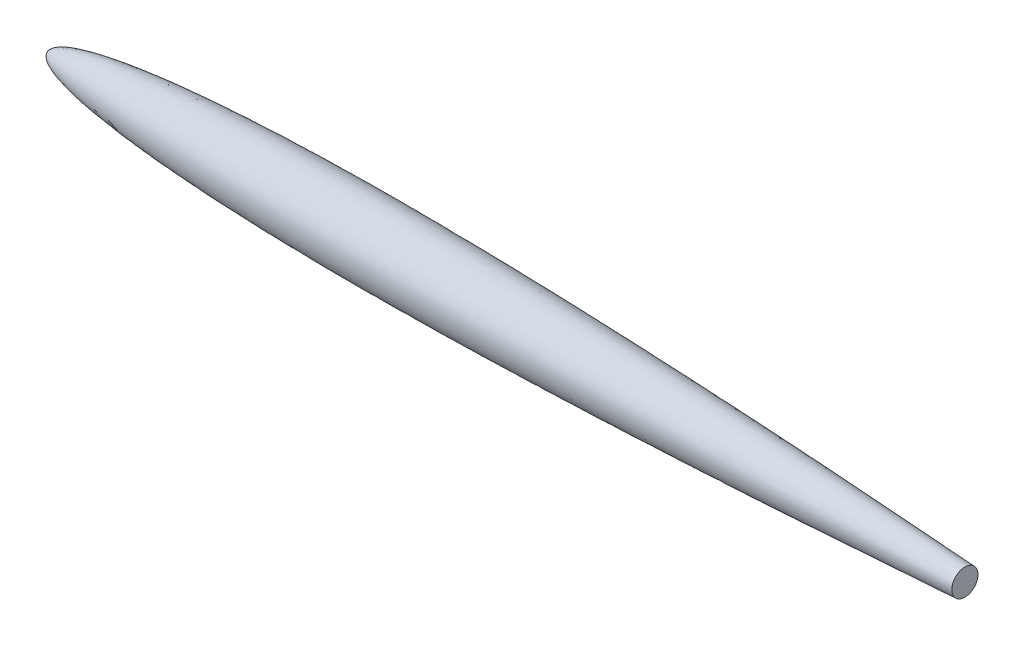
SolidWorks part; units mm, degrees
ref_plane "Front Plane" through (0, 0, 0) normal (0, 0, 1) x (1, 0, 0)
ref_plane "Top Plane" through (0, 0, 0) normal (0, 1, 0) x (1, 0, 0)
ref_plane "Right Plane" through (0, 0, 0) normal (1, 0, 0) x (0, 0, -1)
sketch "rootSketch" plane through (0, 0, 0) normal (0, 1, 0) x (1, 0, 0)
  line L0 (0, 0) -> (12000, 0) construction
  line L1 (2750, -330) -> (2750, 330) construction
  line L2 (0, 0) -> (11000, 0)
  spline S0 degree 4 poles (0, 0) (0.0002, 1.4166) (0.1225, 4.2408) (0.6739, 8.4547) (2.1097, 13.9385) (4.13, 19.1147) (6.6109, 23.9643) (9.9914, 29.3681) (13.8074, 34.3715) (18.0051, 39.0824) (24.0066, 45.0125) (32.3839, 52.2354) (43.384, 60.1944) (57.0761, 68.6181) (73.983, 77.7243) (92.7893, 86.6435) (113.9578, 95.5167) (137.4556, 104.3111) (166.2995, 114.136) (201.291, 124.8338) (243.0702, 136.2047) (291.673, 147.964) (341.2433, 158.778) (390.608, 168.603) (439.7192, 177.609) (500.6517, 187.9807) (573.4692, 199.2826) (658.6122, 211.1866) (758.0842, 223.6079) (859.6848, 234.9957) (963.387, 245.4645) (1069.1706, 255.1028) (1175.0326, 263.8354) (1280.9578, 271.7615) (1386.9346, 278.9616) (1492.954, 285.5022) (1625.577, 292.9263) (1784.8272, 300.7239) (1970.7211, 308.3762) (2183.2661, 315.3874) (2395.8558, 320.8604) (2608.4762, 324.9557) (2821.1167, 327.8069) (3033.7692, 329.5269) (3299.5919, 330.3841) (3618.5808, 329.5138) (3990.7204, 326.0523) (4415.9852, 319.2091) (4841.2016, 309.8574) (5266.3634, 298.3074) (5691.4677, 284.8151) (6116.5132, 269.5907) (6541.4998, 252.8057) (6966.4276, 234.5973) (7391.2968, 215.0715) (7816.1072, 194.3061) (8187.764, 175.0965) (8506.2884, 157.9049) (8771.6988, 143.0951) (8984.0106, 130.9561) (9196.3055, 118.5234) (9382.048, 107.3844) (9541.2445, 97.6474) (9673.9002, 89.4049) (9780.02, 82.7331) (9912.6633, 74.2947) (10032.035, 66.5803) (10138.1364, 59.6277) (10230.971, 53.4713) (10284.0168, 49.9324) (10337.0641, 46.3721) (10390.1043, 42.7909) (10443.153, 39.1874) (10496.1834, 35.5635) (10549.2402, 31.9155) (10602.2495, 28.2488) (10655.3329, 24.5543) (10708.2897, 20.8463) (10761.4536, 17.1004) (10814.2582, 13.3575) (10861.0394, 10.0201) (10900.2084, 7.2123) (10934.3368, 4.7545) (10958.871, 2.9835) (10991.7181, 0.6028) (11015.0262, -1.0918) (11049.9588, -3.6388) (11071.8096, -5.2409) (11099.5819, -7.2784) (11124.1625, -9.0892) (11155.0411, -11.3693) (11188.9639, -13.8862) (11223.5859, -16.4645) (11266.4367, -19.6696) (11318.0968, -23.5545) (11369.6077, -27.4555) (11421.2086, -31.3904) (11472.7604, -35.3439) (11524.3346, -39.3212) (11584.4862, -43.9929) (11670.4236, -50.7243) (11756.3495, -57.532) (11842.2728, -64.4184) (11928.1873, -71.3847) (11996.9163, -77.0066) (12048.459, -81.2601) (12082.8201, -84.1126) (12100, -85.543) knots 0 0 0 0 0 0.000464 0.000929 0.001393 0.001858 0.002287 0.002716 0.003486 0.003922 0.004359 0.005488 0.007118 0.008378 0.009638 0.011797 0.013955 0.015919 0.017882 0.02181 0.025978 0.030146 0.034314 0.038482 0.042518 0.046554 0.054626 0.062698 0.07077 0.079497 0.088224 0.096952 0.105679 0.114406 0.123133 0.13186 0.140587 0.158059 0.17553 0.193002 0.210474 0.227946 0.245418 0.26289 0.280362 0.315306 0.35025 0.385194 0.420137 0.455081 0.490025 0.524969 0.559913 0.594857 0.6298 0.664744 0.699688 0.71716 0.734632 0.752104 0.769576 0.787048 0.795784 0.80452 0.813256 0.821992 0.839464 0.843832 0.8482 0.852567 0.856935 0.861303 0.865671 0.870039 0.874407 0.878775 0.883143 0.887511 0.891879 0.896247 0.900615 0.902799 0.904983 0.907167 0.909351 0.912184 0.915017 0.916433 0.91785 0.920682 0.923515 0.926348 0.929181 0.932013 0.937679 0.943345 0.946177 0.94901 0.954676 0.960341 0.966007 0.977338 0.983003 0.988669 0.994334 1 1 1 1 1 construction
  spline S1 degree 4 poles (0, 0) (0.0002, 1.4166) (0.1225, 4.2408) (0.6739, 8.4547) (2.1097, 13.9385) (4.13, 19.1147) (6.6109, 23.9643) (9.9914, 29.3681) (13.8074, 34.3715) (18.0051, 39.0824) (24.0066, 45.0125) (32.3839, 52.2354) (43.384, 60.1944) (57.0761, 68.6181) (73.983, 77.7243) (92.7893, 86.6435) (113.9578, 95.5167) (137.4556, 104.3111) (166.2995, 114.136) (201.291, 124.8338) (243.0702, 136.2047) (291.673, 147.964) (341.2433, 158.778) (390.608, 168.603) (439.7192, 177.609) (500.6517, 187.9807) (573.4692, 199.2826) (658.6122, 211.1866) (758.0842, 223.6079) (859.6848, 234.9957) (963.387, 245.4645) (1069.1706, 255.1028) (1175.0326, 263.8354) (1280.9578, 271.7615) (1386.9346, 278.9616) (1492.954, 285.5022) (1625.577, 292.9263) (1784.8272, 300.7239) (1970.7211, 308.3762) (2183.2661, 315.3874) (2395.8558, 320.8604) (2608.4762, 324.9557) (2821.1167, 327.8069) (3033.7692, 329.5269) (3299.5919, 330.3841) (3618.5808, 329.5138) (3990.7204, 326.0523) (4415.9852, 319.2091) (4841.2016, 309.8574) (5266.3634, 298.3074) (5691.4677, 284.8151) (6116.5132, 269.5907) (6541.4998, 252.8057) (6966.4276, 234.5973) (7391.2968, 215.0715) (7816.1072, 194.3061) (8187.764, 175.0965) (8506.2884, 157.9049) (8771.6988, 143.0951) (8984.0106, 130.9561) (9196.3055, 118.5234) (9382.048, 107.3844) (9541.2445, 97.6474) (9673.9002, 89.4049) (9780.02, 82.7331) (9912.6633, 74.2947) (10032.035, 66.5803) (10138.1364, 59.6277) (10230.971, 53.4713) (10284.0168, 49.9324) (10337.0641, 46.3721) (10390.1043, 42.7909) (10443.153, 39.1874) (10496.1834, 35.5635) (10549.2402, 31.9155) (10602.2495, 28.2488) (10655.3329, 24.5543) (10708.2897, 20.8463) (10761.4536, 17.1004) (10814.2582, 13.3575) (10861.0394, 10.0201) (10900.2084, 7.2123) (10934.3368, 4.7545) (10958.871, 2.9835) (10981.8033, 1.3214) (10993.9727, 0.438) (11000, 0) knots 0 0 0 0 0 0.000464 0.000929 0.001393 0.001858 0.002287 0.002716 0.003486 0.003922 0.004359 0.005488 0.007118 0.008378 0.009638 0.011797 0.013955 0.015919 0.017882 0.02181 0.025978 0.030146 0.034314 0.038482 0.042518 0.046554 0.054626 0.062698 0.07077 0.079497 0.088224 0.096952 0.105679 0.114406 0.123133 0.13186 0.140587 0.158059 0.17553 0.193002 0.210474 0.227946 0.245418 0.26289 0.280362 0.315306 0.35025 0.385194 0.420137 0.455081 0.490025 0.524969 0.559913 0.594857 0.6298 0.664744 0.699688 0.71716 0.734632 0.752104 0.769576 0.787048 0.795784 0.80452 0.813256 0.821992 0.839464 0.843832 0.8482 0.852567 0.856935 0.861303 0.865671 0.870039 0.874407 0.878775 0.883143 0.887511 0.891879 0.896247 0.900615 0.902799 0.904983 0.907167 0.909351 0.909351 0.909351 0.909351 0.909351
  point P5 (2750, 0)
  dimension "rootQuarterChord" = 2750
  dimension "rootMaxThickness" = 660
revolve "Revolve1" add sketch "rootSketch" angle 360 about L0
ref_plane "Plane1" through (9020, 0, 0) normal (1, 0, 0) x (0, 0, -1)
sketch "cutSketch" plane through (9020, 0, 0) normal (1, 0, 0) x (0, 0, -1)
  circle A0 centre (0, 0) radius 330
  dimension "cutDiameter" = 660
extrude "Cut-Extrude1" cut sketch "cutSketch" along normal through all
equation "\"chord\"= 11.00"
equation "\"NACAairfoil\"= 0006"
equation "\"tailCutoffPercentage\"= 0.18"
equation "\"rootQuarterChord@rootSketch\"=\"chord\"/4"
equation "\"rootMaxThickness@rootSketch\"=\"rootQuarterChord@rootSketch\"*4*\"NACAairfoil\"/100"
equation "\"cutDiameter@cutSketch\"=\"rootMaxThickness@rootSketch\""
equation "\"cutChord@Plane1\"= \"rootQuarterChord@rootSketch\" * 4 * ( 1 - \"tailCutoffPercentage\" )"
